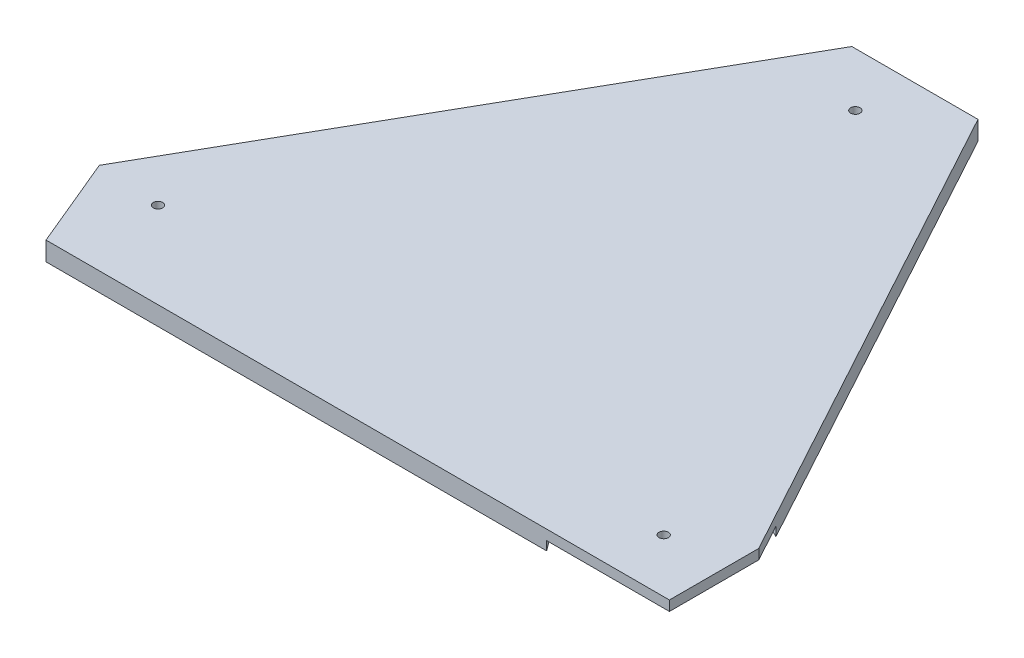
SolidWorks part; units mm, degrees
material "Cedar"
ref_plane "Front Plane" through (0, 0, 0) normal (0, 0, 1) x (1, 0, 0)
ref_plane "Top Plane" through (0, 0, 0) normal (0, 1, 0) x (1, 0, 0)
ref_plane "Right Plane" through (0, 0, 0) normal (1, 0, 0) x (0, 0, -1)
sketch "Sketch1" plane through (0, 0, 0) normal (0, 1, 0) x (1, 0, 0)
  line L0 (0, 0) -> (-523.875, 0)
  line L1 (-523.875, 0) -> (-555.8494, 76.7944)
  line L2 (-555.8494, 76.7944) -> (-326.1382, 479.425)
  line L3 (-326.1382, 479.425) -> (-220.1186, 479.425)
  line L4 (-220.1186, 479.425) -> (0, 75.0824)
  line L5 (0, 75.0824) -> (0, 0)
  dimension "D1" = 523.875
  dimension "D2" = 83.185
  dimension "D3" = 75.0824
  dimension "D4" = 460.375
  dimension "D5" = 106.0196
  dimension "D6" = 463.55
  dimension "D7" = 479.425
extrude "Boss-Extrude1" add sketch "Sketch1" along normal blind 15.875
sketch "Sketch2" plane through (0, 15.875, 0) normal (0, 1, 0) x (1, 0, 0)
  line L0 (-220.1186, 479.425) -> (-326.1382, 479.425) construction
  line L1 (-523.875, 0) -> (0, 0) construction
  line L2 (0, 0) -> (0, 75.0824) construction
  circle A0 centre (-278.1068, 434.34) radius 3.9688
  circle A1 centre (-502.2046, 72.4408) radius 3.9688
  circle A2 centre (-49.7332, 44.9326) radius 3.9687
  dimension "D1" = 7.9375
  dimension "D2" = 7.9375
  dimension "D3" = 7.9375
  dimension "D6" = 72.4408
  dimension "D8" = 44.9326
  dimension "D4" = 45.085
  dimension "D5" = 48.0314
  dimension "D7" = 53.6448
  dimension "D9" = 49.7332
extrude "Cut-Extrude1" cut sketch "Sketch2" against normal through all
sketch "Sketch3" plane through (0, 0, 0) normal (0, -1, 0) x (1, 0, 0)
  circle A0 centre (-502.2046, -72.4408) radius 63.5
  circle A3 centre (-49.7332, -44.9326) radius 69.85
  circle A4 centre (-278.1068, -434.34) radius 63.5
  dimension "D1" = 127
  dimension "D2" = 139.7
  dimension "D3" = 127
extrude "Cut-Extrude2" cut sketch "Sketch3" against normal blind 7.493
